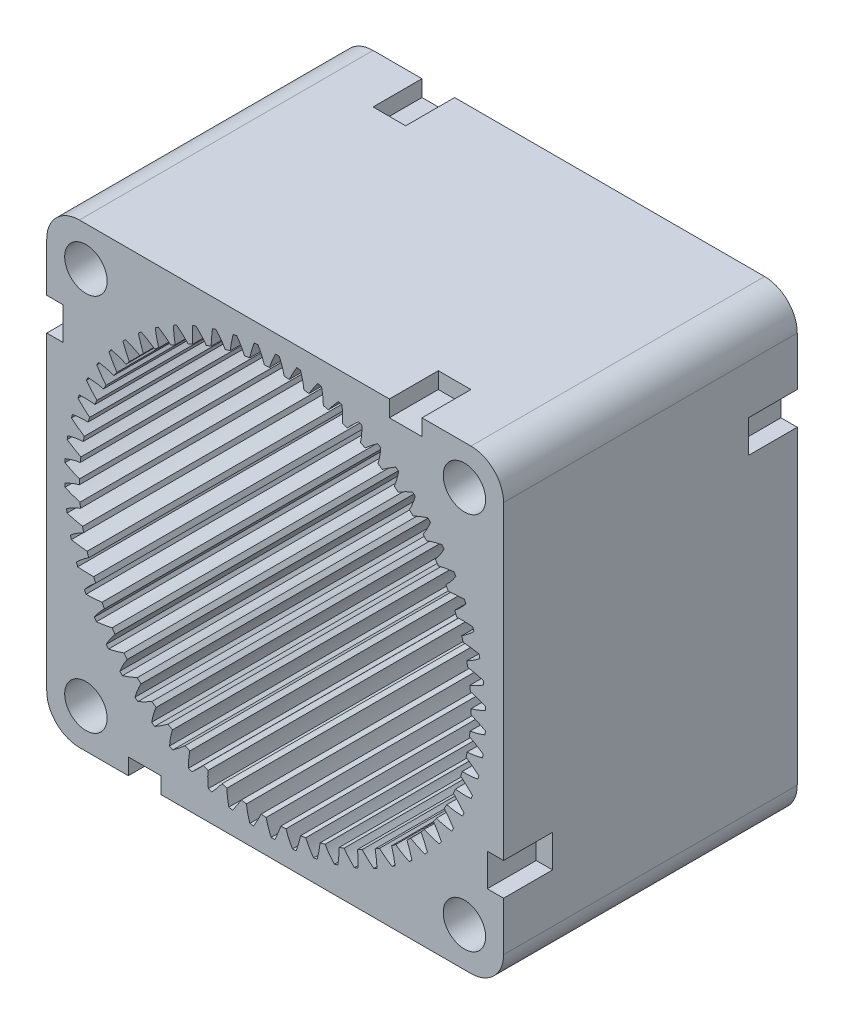
SolidWorks part; units mm, degrees
other "标注1"
sketch "草图9" plane through (-21, -21, 36) normal (-0.2153, -0.0648, 0.9744) x (0.3119, -0.9501, 0.0057)
other "标注2"
sketch "草图20" plane through (-30, -30, 20) normal (-0.0347, -0.0183, 0.9992) x (0.9994, -0.0065, 0.0346)
ref_plane "前视基准面" through (0, 0, 0) normal (0, 0, 1) x (1, 0, 0)
ref_plane "上视基准面" through (0, 0, 0) normal (0, 1, 0) x (1, 0, 0)
ref_plane "右视基准面" through (0, 0, 0) normal (1, 0, 0) x (0, 0, -1)
sketch "草图1" plane through (0, 0, 0) normal (0, 0, 1) x (1, 0, 0)
  line L5 (-21.1128, -21.1128) -> (20.8872, 20.8872) construction
  line L6 (-21, 21) -> (21, -21) construction
  line L7 (14, 14) -> (-14, 14)
  line L8 (14, 14) -> (14, -14)
  line L9 (14, -14) -> (-14, -14)
  line L10 (-14, 14) -> (-14, -14)
  line L11 (0, -14) -> (0, 14) construction
  line L12 (14, 0) -> (-14, 0) construction
  circle A9 centre (0, 0) radius 30
  circle A18 centre (-26, 0) radius 2.2
  circle A19 centre (-22.5167, 13) radius 2.2
  circle A20 centre (-13, 22.5167) radius 2.2
  circle A21 centre (0, 26) radius 2.2
  circle A22 centre (13, 22.5167) radius 2.2
  circle A23 centre (22.5167, 13) radius 2.2
  circle A24 centre (26, 0) radius 2.2
  circle A25 centre (22.5167, -13) radius 2.2
  circle A26 centre (13, -22.5167) radius 2.2
  circle A27 centre (0, -26) radius 2.2
  circle A28 centre (-13, -22.5167) radius 2.2
  circle A29 centre (-22.5167, -13) radius 2.2
  circle A30 centre (11.6, 11.6) radius 1.3
  circle A31 centre (11.6, -11.6) radius 1.3
  circle A32 centre (-11.6, -11.6) radius 1.3
  circle A33 centre (-11.6, 11.6) radius 1.3
  point P31 (0, 0)
  point P37 (0, 0)
  point P48 (0, 0)
  dimension "D1" = 28
  dimension "D4" = 60
  dimension "D6" = 28
  dimension "D2" = 4.4
  dimension "D3" = 26
  dimension "D9" = 2.6
  dimension "D7" = 11.6
  dimension "D8" = 11.6
  dimension "D5" = 12
  dimension "D10" = 4
extrude "凸台-拉伸1" add sketch "草图1" along normal blind 18 contours L7 L10 L9 L8 A33 A32 A31 A30
sketch "草图6" plane through (0, 0, 0) normal (0, 0, 1) x (1, 0, 0)
  line L0 (0, 0) -> (11.6522, 0) construction
  line L1 (0, 0) -> (35.0568, 1.4114) construction
  line L2 (0, 0) -> (12.3986, 0.1848) construction
  circle A0 centre (0, 0) radius 12.4 construction
  circle A1 centre (0, 0) radius 5 construction
  circle A2 centre (0, 0) radius 11.6522 construction
  circle A3 centre (0, 0) radius 12.9 construction
  arc A4 (12.2091, -2.1677) -> (12.3986, 0.1848) centre (0, 0) cw construction
  circle A5 centre (0, 0) radius 10
  circle A7 centre (0, 0) radius 12
  arc A8 (12.8844, 0.634) -> (12.8936, 0.407) centre (0, 0) cw
  spline S0 degree 4 poles (11.6522, 0) (11.6616, 0.0002) (11.6881, 0.0014) (11.738, 0.0063) (11.8191, 0.0179) (11.9217, 0.038) (12.0533, 0.07) (12.2066, 0.1153) (12.373, 0.1732) (12.5514, 0.2446) (12.7269, 0.3232) (12.8995, 0.4085) (13.0688, 0.4995) (13.2708, 0.6168) (13.5084, 0.7672) (13.7788, 0.9569) (14.0765, 1.188) (14.3692, 1.4399) (14.6484, 1.7013) (14.9193, 1.98) (15.1736, 2.26) (15.4255, 2.565) (15.6518, 2.8538) (15.891, 3.192) (16.0799, 3.4694) (16.3133, 3.8501) (16.4462, 4.0792) (16.5962, 4.3523) (16.6598, 4.476) (16.699, 4.5522) knots 0 0 0 0 0 0.005377 0.015084 0.028532 0.04661 0.064855 0.092111 0.119476 0.146842 0.174209 0.201575 0.228941 0.256307 0.307035 0.361767 0.4165 0.471232 0.525964 0.580697 0.635429 0.690161 0.744894 0.799626 0.854358 0.909091 0.954545 1 1 1 1 1 construction
  spline S1 degree 4 poles (11.6522, 0) (11.6616, 0.0002) (11.6881, 0.0014) (11.738, 0.0063) (11.8191, 0.0179) (11.9217, 0.038) (12.0533, 0.07) (12.2066, 0.1153) (12.373, 0.1732) (12.5514, 0.2446) (12.7269, 0.3232) (12.8995, 0.4085) (13.0688, 0.4995) (13.2708, 0.6168) (13.5084, 0.7672) (13.7788, 0.9569) (14.0765, 1.188) (14.3692, 1.4399) (14.6484, 1.7013) (14.9193, 1.98) (15.1736, 2.26) (15.4255, 2.565) (15.6518, 2.8538) (15.891, 3.192) (16.0799, 3.4694) (16.2627, 3.7675) (16.3497, 3.9143) (16.3935, 3.99) knots 0 0 0 0 0 0.005377 0.015084 0.028532 0.04661 0.064855 0.092111 0.119476 0.146842 0.174209 0.201575 0.228941 0.256307 0.307035 0.361767 0.4165 0.471232 0.525964 0.580697 0.635429 0.690161 0.744894 0.799626 0.854358 0.909091 0.909091 0.909091 0.909091 0.909091
  spline S2 degree 4 poles (10.7591, 1.1455) (10.7749, 1.1464) (10.8193, 1.1479) (10.9033, 1.1465) (11.0402, 1.138) (11.294, 1.1093) (11.5964, 1.0534) (11.9345, 0.9693) (12.2934, 0.8583) (12.597, 0.7506) (12.8965, 0.6315) (13.1916, 0.5022) (13.5444, 0.3337) (13.9617, 0.1142) (14.4382, -0.1652) (14.9671, -0.5121) (15.4886, -0.8917) (15.9917, -1.2931) (16.4786, -1.7176) (16.9457, -2.158) (17.3994, -2.6217) (17.7749, -3.0327) (18.096, -3.4089) (18.3409, -3.7056) (18.559, -3.9849) (18.7682, -4.2537) (19.0042, -4.5806) (19.1291, -4.7572) (19.2123, -4.8777) knots 0 0 0 0 0 0.005377 0.015084 0.028532 0.04661 0.092111 0.119476 0.146842 0.174209 0.201575 0.228941 0.256307 0.307035 0.361767 0.4165 0.471232 0.525964 0.580697 0.635429 0.690161 0.744894 0.77226 0.799626 0.826992 0.854358 0.909091 0.909091 0.909091 0.909091 0.909091
  point P6 (30.6834, 1.2647)
  dimension "D1" = 24.8
  dimension "D2" = 10
  dimension "D3" = 25.8
  dimension "D4" = 23.3044
  dimension "D6" = 24
  dimension "D7" = 20
  dimension "D5" = 1.452
extrude "切除-拉伸1" cut sketch "草图6" along normal through all
pattern_circular "阵列(圆周)1" count 62 over 360 about axis through (0, 0, 0) along (0, 0, -1) of "切除-拉伸1"
sketch "草图14" [suppressed] plane through (0, 0, 18) normal (0, 0, 1) x (1, 0, 0)
  circle A0 centre (0, 0) radius 11.9325
  dimension "D1" = 25.8
fillet "圆角2" radius 2 4 edges at (14, -14, 9) (-14, -14, 9) (-14, 14, 9) (14, 14, 9)
sketch "草图23" plane through (0, 0, 0) normal (0, 0, -1) x (-1, 0, 0)
  line L0 (-14, 12) -> (-14, -12) construction
  line L1 (-14, 9) -> (-13, 9)
  line L2 (-14, 9) -> (-14, 7)
  line L3 (-14, 7) -> (-13, 7)
  line L4 (-13, 9) -> (-13, 7)
  line L5 (-12, 14) -> (12, 14) construction
  line L6 (9, 14) -> (7, 14)
  line L7 (9, 14) -> (9, 13)
  line L8 (9, 13) -> (7, 13)
  line L9 (7, 14) -> (7, 13)
  line L10 (14, -9) -> (14, -7)
  line L11 (14, -9) -> (13, -9)
  line L12 (13, -9) -> (13, -7)
  line L13 (14, -7) -> (13, -7)
  line L14 (-9, -14) -> (-7, -14)
  line L15 (-9, -14) -> (-9, -13)
  line L16 (-9, -13) -> (-7, -13)
  line L17 (-7, -14) -> (-7, -13)
  point P23 (0, 0)
  dimension "D1" = 1
  dimension "D2" = 2
  dimension "D3" = 5
  dimension "D4" = 4
extrude "切除-拉伸14" cut sketch "草图23" against normal blind 3
sketch "草图24" plane through (0, 0, 18) normal (0, 0, 1) x (1, 0, 0)
  line L0 (-14, 9) -> (-13, 9)
  line L1 (-14, 9) -> (-14, 7)
  line L2 (-14, 7) -> (-13, 7)
  line L3 (-13, 9) -> (-13, 7)
  line L16 (-14, 12) -> (-14, -12) construction
  line L17 (12, 14) -> (-12, 14) construction
  line L18 (9, 14) -> (9, 13)
  line L19 (9, 13) -> (7, 13)
  line L20 (7, 14) -> (7, 13)
  line L21 (9, 14) -> (7, 14)
  line L22 (14, -9) -> (13, -9)
  line L23 (13, -9) -> (13, -7)
  line L24 (14, -7) -> (13, -7)
  line L25 (14, -9) -> (14, -7)
  line L26 (-9, -14) -> (-9, -13)
  line L27 (-9, -13) -> (-7, -13)
  line L28 (-7, -14) -> (-7, -13)
  line L29 (-9, -14) -> (-7, -14)
  point P16 (0.2043, -0.1277)
  point P24 (0, 0)
  dimension "D1" = 1
  dimension "D2" = 2
  dimension "D3" = 5
  dimension "D4" = 4
extrude "切除-拉伸15" cut sketch "草图24" against normal blind 3
extrude "凸台-拉伸5" [suppressed] add sketch "草图14" along normal mid plane 4
chamfer "倒角6" [suppressed] distance 1 angle 45
sketch "草图15" [suppressed] plane through (0, 0, 20) normal (0, 0, 1) x (1, 0, 0)
  circle A0 centre (0, 0) radius 21.285
  circle A1 centre (0, 0) radius 20
  dimension "D1" = 42.57
  dimension "D2" = 40
extrude "切除-拉伸8" [suppressed] cut sketch "草图15" against normal blind 2
sketch "草图16" [suppressed] plane through (0, 0, 20) normal (0, 0, 1) x (1, 0, 0)
  circle A0 centre (0, 0) radius 18.5
  dimension "D1" = 37
extrude "切除-拉伸9" [suppressed] cut sketch "草图16" against normal up to next
chamfer "倒角7" [suppressed] distance 3 angle 45
chamfer "倒角2" [suppressed] distance 0.5 angle 45
chamfer "倒角3" [suppressed] distance 0.5 angle 45
sketch "草图8" [suppressed] plane through (0, 0, 28) normal (0, 0, 1) x (1, 0, 0)
  circle A0 centre (0, 0) radius 19.2188
  dimension "D1" = 25.8
extrude "切除-拉伸3" [suppressed] cut sketch "草图8" against normal blind 23
sketch "草图17" [suppressed] plane through (0, 0, 0) normal (0, 0, -1) x (-1, 0, 0)
  circle A0 centre (0, 0) radius 20
  dimension "D1" = 25
extrude "切除-拉伸10" [suppressed] cut sketch "草图17" against normal blind 10
sketch "草图18" [suppressed] plane through (0, 0, 18) normal (0, 0, 1) x (1, 0, 0)
  circle A0 centre (-26, 0) radius 2.2
  circle A1 centre (0, 26) radius 2.2
  circle A2 centre (26, 0) radius 2.2
  circle A3 centre (0, -26) radius 2.2
  point P12 (0, 0)
  dimension "D1" = 4
extrude "凸台-拉伸6" [suppressed] add sketch "草图18" against normal through all
sketch "草图19" [suppressed] plane through (0, 0, 18) normal (0, 0, 1) x (1, 0, 0)
  line L0 (-36.8786, 0) -> (37.8167, 0) construction
  line L2 (-37.7449, 3.25) -> (-24.9449, 3.25)
  line L3 (-37.7449, 3.25) -> (-37.7449, -3.25)
  line L4 (-37.7449, -3.25) -> (-24.9449, -3.25)
  line L5 (-24.9449, 3.25) -> (-24.9449, -3.25)
  line L6 (-37.7449, 3.25) -> (-24.9449, -3.25) construction
  line L7 (-37.7449, -3.25) -> (-24.9449, 3.25) construction
  line L8 (-27.5449, 6.95) -> (-24.9449, 6.95)
  line L9 (-27.5449, 6.95) -> (-27.5449, 3.25)
  line L10 (-27.5449, 3.25) -> (-24.9449, 3.25)
  line L11 (-24.9449, 6.95) -> (-24.9449, 3.25)
  line L12 (-27.5449, 6.95) -> (-24.9449, 3.25) construction
  line L13 (-27.5449, 3.25) -> (-24.9449, 6.95) construction
  point P3 (-31.3449, 0)
  point P8 (-29.9449, 0)
  point P9 (-43.345, 0.7504)
  point P10 (-26.2449, 5.1)
  dimension "D1" = 6.5
  dimension "D2" = 12.8
  dimension "D3" = 5
  dimension "D4" = 3.7
  dimension "D5" = 2.6
extrude "切除-拉伸12" [suppressed] cut sketch "草图19" against normal blind 6 contours L5 L2 L4 | L11 L8 L9 L2
equation "\"m\"= 0.40"
equation "\"z\"= 62"
equation "\"a\"= 20"
equation "\"d\"= \"m\" * \"z\""
equation "\"da\"= \"m\" * ( \"z\" - 2 )"
equation "\"df\"= \"d\" + 2.5 * \"m\""
equation "\"db\"= \"d\" * cos ( \"a\" )"
equation "\"s\"= pi * \"m\" / 2"
equation "\"D1@草图6\"=\"d\""
equation "\"D3@草图6\"=\"df\""
equation "\"D4@草图6\"=\"db\""
equation "\"D6@草图6\"=\"da\""
equation "\"D1@草图8\"=\"df\""
equation "\"sr\"= 360 / \"z\" / 4"
equation "\"D5@草图6\"=\"sr\""
equation "\"D1@草图14\"=\"df\""
equation "\"D1@阵列(圆周)1\"=\"z\""
equation "\"D1@草图17\"=\"da\"+1"
